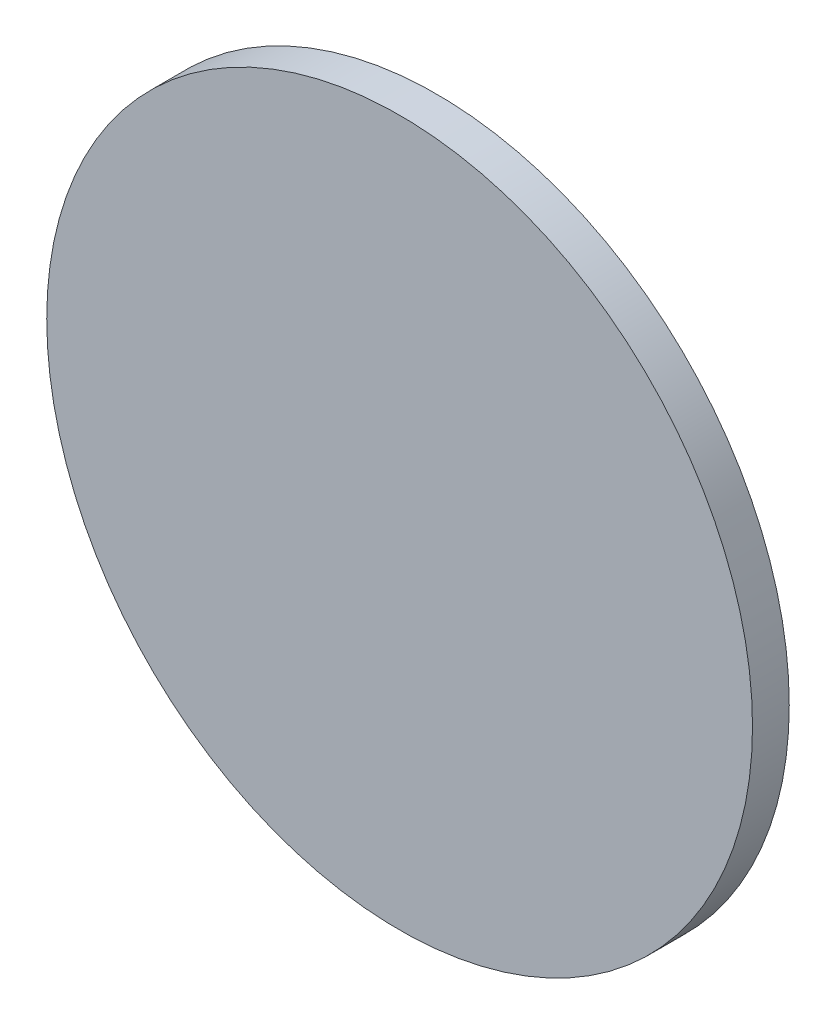
SolidWorks part; units mm, degrees
ref_plane "Plan de face" through (0, 0, 0) normal (0, 0, 1) x (1, 0, 0)
ref_plane "Plan de dessus" through (0, 0, 0) normal (0, 1, 0) x (1, 0, 0)
ref_plane "Plan de droite" through (0, 0, 0) normal (1, 0, 0) x (0, 0, -1)
sketch "Esquisse1" plane through (0, 0, 0) normal (0, 0, 1) x (1, 0, 0)
  circle A0 centre (0, 0) radius 96
  dimension "D1" = 192
extrude "Boss.-Extru.1" add sketch "Esquisse1" along normal blind 10
